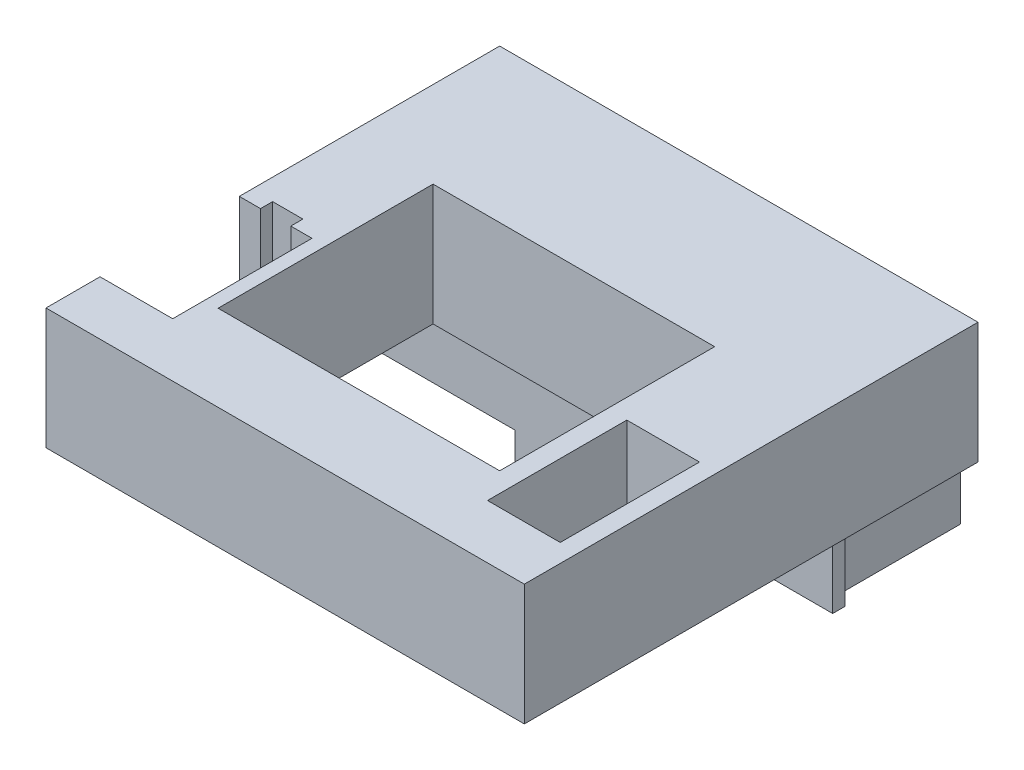
SolidWorks part; units mm, degrees
ref_plane "Alzado" through (0, 0, 0) normal (0, 0, 1) x (1, 0, 0)
ref_plane "Planta" through (0, 0, 0) normal (0, 1, 0) x (1, 0, 0)
ref_plane "Vista lateral" through (0, 0, 0) normal (1, 0, 0) x (0, 0, -1)
ref_plane "Plano1" through (0, 13.27, 0) normal (0, 1, 0) x (1, 0, 0)
sketch "Croquis1" plane through (0, 13.27, 0) normal (0, 1, 0) x (1, 0, 0)
  line L0 (-91, 0) -> (-91, -74.927)
  line L1 (-91, -74.927) -> (-12, -74.927)
  line L2 (-12, -74.927) -> (-12, 0)
  line L3 (-12, 0) -> (-91, 0)
extrude "Saliente-Extruir1" add sketch "Croquis1" against normal blind 20
sketch "Croquis2" plane through (0, -6.73, 0) normal (0, -1, 0) x (1, 0, 0)
  line L0 (-14.879, 0) -> (-88.121, 0)
  line L1 (-88.121, 0) -> (-88.121, 20)
  line L2 (-88.121, 20) -> (-89.001, 20)
  line L3 (-89.001, 20) -> (-89.001, 22)
  line L4 (-89.001, 22) -> (-14, 22)
  line L5 (-14, 22) -> (-14, 20)
  line L6 (-14, 20) -> (-14.879, 20)
  line L7 (-14.879, 20) -> (-14.879, 0)
extrude "Saliente-Extruir2" add sketch "Croquis2" along normal blind 10.312
sketch "Croquis3" plane through (0, -17.042, 0) normal (0, -1, 0) x (1, 0, 0)
  line L0 (-89.001, 22) -> (-14, 22)
  line L1 (-14, 22) -> (-14, 20)
  line L2 (-14, 20) -> (-89.001, 20)
  line L3 (-89.001, 20) -> (-89.001, 22)
extrude "Saliente-Extruir3" add sketch "Croquis3" along normal blind 8.358
sketch "Croquis4" plane through (0, 0, 22) normal (0, 0, 1) x (1, 0, 0)
  line L0 (-38.49, -18.4) -> (-38.49, -25.4)
  line L1 (-38.49, -25.4) -> (-14, -25.4)
  line L2 (-14, -25.4) -> (-14, -18.4)
  line L3 (-14, -18.4) -> (-38.49, -18.4)
extrude "Cortar-Extruir1" cut sketch "Croquis4" against normal through all
sketch "Croquis5" plane through (0, 0, 22) normal (0, 0, 1) x (1, 0, 0)
  line L0 (-66.5, -18.4) -> (-89.001, -18.4)
  line L1 (-89.001, -18.4) -> (-89.001, -25.4)
  line L2 (-89.001, -25.4) -> (-66.5, -25.4)
  line L3 (-66.5, -25.4) -> (-66.5, -18.4)
extrude "Cortar-Extruir2" cut sketch "Croquis5" against normal through all
sketch "Croquis6" plane through (0, -6.73, 0) normal (0, -1, 0) x (1, 0, 0)
  line L0 (-91, 66.003) -> (-91, 42.998)
  line L1 (-91, 42.998) -> (-78.998, 42.998)
  line L2 (-78.998, 42.998) -> (-78.998, 66.003)
  line L3 (-78.998, 66.003) -> (-91, 66.003)
extrude "Cortar-Extruir3" cut sketch "Croquis6" against normal through all
sketch "Croquis7" plane through (0, 0, 20) normal (0, 0, -1) x (-1, 0, 0)
  line L0 (39.293, -17.042) -> (63.707, -17.042)
  line L1 (63.707, -17.042) -> (63.707, -23.067)
  line L2 (63.707, -23.067) -> (39.293, -23.067)
  line L3 (39.293, -23.067) -> (39.293, -17.042)
extrude "Saliente-Extruir4" add sketch "Croquis7" along normal blind 20
sketch "Croquis8" plane through (0, 13.27, 0) normal (0, 1, 0) x (-1, 0, 0)
  line L0 (76.753, 25.248) -> (76.753, 60.753)
  line L1 (76.753, 60.753) -> (30.248, 60.753)
  line L2 (30.248, 60.753) -> (30.248, 25.248)
  line L3 (30.248, 25.248) -> (76.753, 25.248)
extrude "Cortar-Extruir4" cut sketch "Croquis8" against normal through all
sketch "Croquis9" plane through (0, -6.73, 0) normal (0, -1, 0) x (1, 0, 0)
  line L0 (-27.003, 42.998) -> (-14.998, 42.998)
  line L1 (-14.998, 42.998) -> (-14.998, 66.003)
  line L2 (-14.998, 66.003) -> (-27.003, 66.003)
  line L3 (-27.003, 66.003) -> (-27.003, 42.998)
extrude "Cortar-Extruir5" cut sketch "Croquis9" against normal through all
sketch "Croquis10" plane through (0, -23.067, 0) normal (0, -1, 0) x (1, 0, 0)
  line L0 (-43.88, 17.015) -> (-59.12, 17.015)
  line L1 (-59.12, 17.015) -> (-59.12, 1.624)
  line L2 (-59.12, 1.624) -> (-43.88, 1.624)
  line L3 (-43.88, 1.624) -> (-43.88, 17.015)
extrude "Cortar-Extruir6" cut sketch "Croquis10" against normal blind 35.07
sketch "Croquis11" plane through (0, -17.042, 0) normal (0, -1, 0) x (1, 0, 0)
  line L0 (-17.336, 3.074) -> (-17.336, 16.926)
  line L1 (-17.336, 16.926) -> (-37.835, 16.926)
  line L2 (-37.835, 16.926) -> (-37.835, 3.074)
  line L3 (-37.835, 3.074) -> (-17.336, 3.074)
extrude "Cortar-Extruir7" cut sketch "Croquis11" against normal blind 10.312
sketch "Croquis12" plane through (0, -17.042, 0) normal (0, -1, 0) x (1, 0, 0)
  line L0 (-65.236, 16.926) -> (-85.736, 16.926)
  line L1 (-85.736, 16.926) -> (-85.736, 3.074)
  line L2 (-85.736, 3.074) -> (-65.236, 3.074)
  line L3 (-65.236, 3.074) -> (-65.236, 16.926)
extrude "Cortar-Extruir8" cut sketch "Croquis12" against normal blind 10.312
sketch "Croquis13" plane through (0, 0, 42.998) normal (0, 0, 1) x (1, 0, 0)
  line L0 (55, 13.27) -> (-55, 13.27) construction
  line L1 (-87.5, 13.27) -> (-82.5, 13.27)
  line L2 (-87.5, 13.27) -> (-87.5, 3.27)
  line L3 (-87.5, 3.27) -> (-82.5, 3.27)
  line L4 (-82.5, 13.27) -> (-82.5, 3.27)
  line L5 (-91, -6.73) -> (-91, 13.27) construction
  dimension "D1" = 5
  dimension "D2" = 10
  dimension "D3" = 3.5
extrude "Cortar-Extruir9" cut sketch "Croquis13" against normal blind 2
